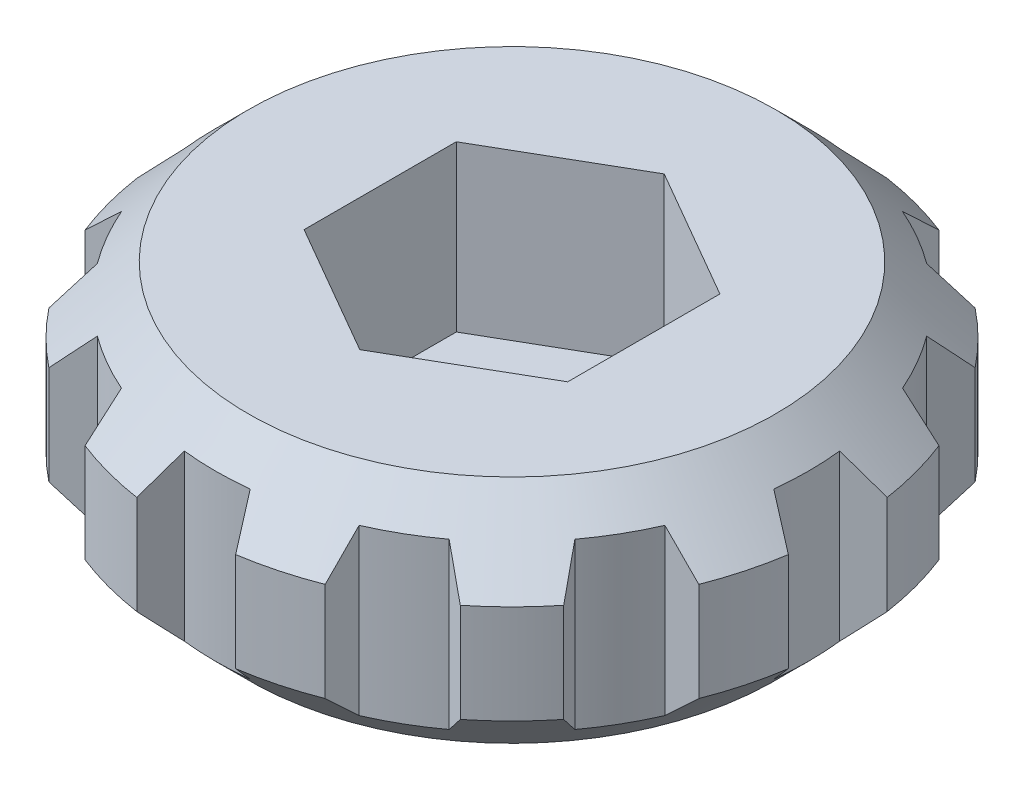
SolidWorks part; units mm, degrees
material "PET"
ref_plane "Přední rovina" through (0, 0, 0) normal (0, 0, 1) x (1, 0, 0)
ref_plane "Horní rovina" through (0, 0, 0) normal (0, 1, 0) x (1, 0, 0)
ref_plane "Pravá rovina" through (0, 0, 0) normal (1, 0, 0) x (0, 0, -1)
sketch "Skica1" plane through (0, 0, 0) normal (1, 0, 0) x (0, 0, -1)
  line L0 (0, 0) -> (0, 25.9843) construction
  line L1 (2.75, 0) -> (8, 0)
  line L2 (2.75, 0) -> (2.75, 7)
  line L3 (2.75, 7) -> (8, 7)
  line L4 (10, 2) -> (10, 5)
  line L5 (8, 7) -> (10, 5)
  line L6 (8, 0) -> (10, 2)
  point P1 (10, 7)
  point P3 (10, 0)
  dimension "D1" = 5.5
  dimension "D2" = 20
  dimension "D3" = 7
revolve "Rotovat1" add sketch "Skica1" angle 360 about L0
sketch "Skica2" plane through (0, 7, 0) normal (0, 1, 0) x (1, 0, 0)
  line L1 (-4, -2.3094) -> (0, -4.6188)
  line L2 (0, -4.6188) -> (4, -2.3094)
  line L3 (4, -2.3094) -> (4, 2.3094)
  line L4 (4, 2.3094) -> (0, 4.6188)
  line L5 (0, 4.6188) -> (-4, 2.3094)
  line L6 (-4, 2.3094) -> (-4, -2.3094)
  circle A0 centre (0, 0) radius 4 construction
  dimension "D1" = 8
extrude "Odebrat vysunutím1" cut sketch "Skica2" against normal offset from surface (5 mm away) 2 up to face at (0, 0, -8)
sketch "Skica3" plane through (0, 7, 0) normal (0, 1, 0) x (1, 0, 0)
  line L0 (-1, 8.9443) -> (-1.5, 9.8869)
  line L1 (1.5, 9.8869) -> (1, 8.9443)
  line L2 (0, 0) -> (0, 13.3324) construction
  arc A0 (1, 8.9443) -> (-1, 8.9443) centre (0, 0) ccw
  circle A1 centre (0, 0) radius 8 construction
  circle A2 centre (0, 0) radius 10 construction
  arc A3 (1.5, 9.8869) -> (-1.5, 9.8869) centre (0, 0) ccw
  dimension "D1" = 1
  dimension "D2" = 2
  dimension "D3" = 3
extrude "Odebrat vysunutím2" cut sketch "Skica3" against normal through all
pattern_circular "Kruhové pole1" count 12 over 360 about axis through (0, 0, 0) along (0, 1, 0) of "Odebrat vysunutím2"
